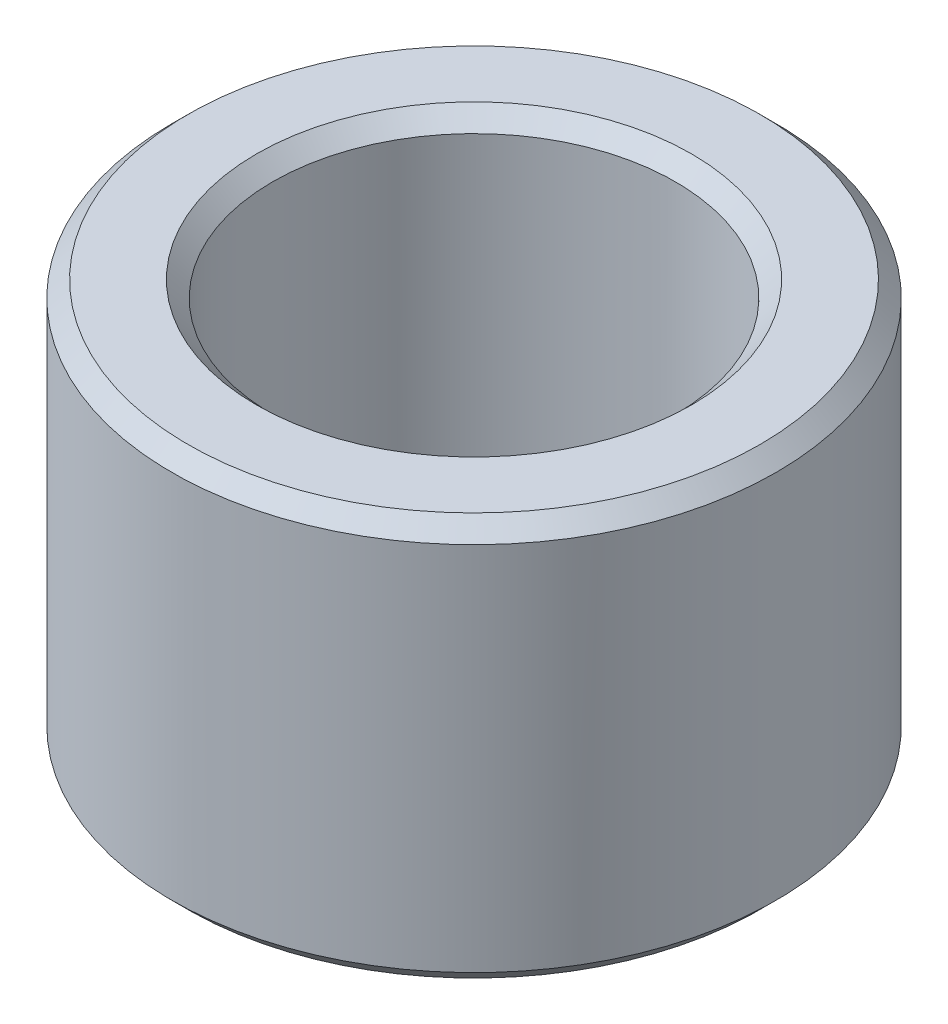
SolidWorks part; units mm, degrees
ref_plane "Front" through (0, 0, 0) normal (0, 0, 1) x (1, 0, 0)
ref_plane "Top" through (0, 0, 0) normal (0, 1, 0) x (1, 0, 0)
ref_plane "Right" through (0, 0, 0) normal (1, 0, 0) x (0, 0, -1)
sketch "Sketch1" plane through (0, 0, 0) normal (0, 0, 1) x (1, 0, 0)
  line L0 (0, 2.8226) -> (0, -2.8226) construction
  line L1 (3.175, 3.175) -> (3.175, -3.175)
  line L2 (3.175, -3.175) -> (4.7625, -3.175)
  line L3 (4.7625, -3.175) -> (4.7625, 3.175)
  line L4 (4.7625, 3.175) -> (3.175, 3.175)
  point P7 (3.175, 0)
  dimension "D1" = 6.35
  dimension "D2" = 6.35
  dimension "D3" = 9.525
revolve "Revolve1" add sketch "Sketch1" angle 360 about L0
chamfer "Chamfer1" distance 0.254 angle 45 4 edges at (-3.175, -3.175, 0) (-4.7625, -3.175, 0) (-4.7625, 3.175, 0) (-3.175, 3.175, 0)
